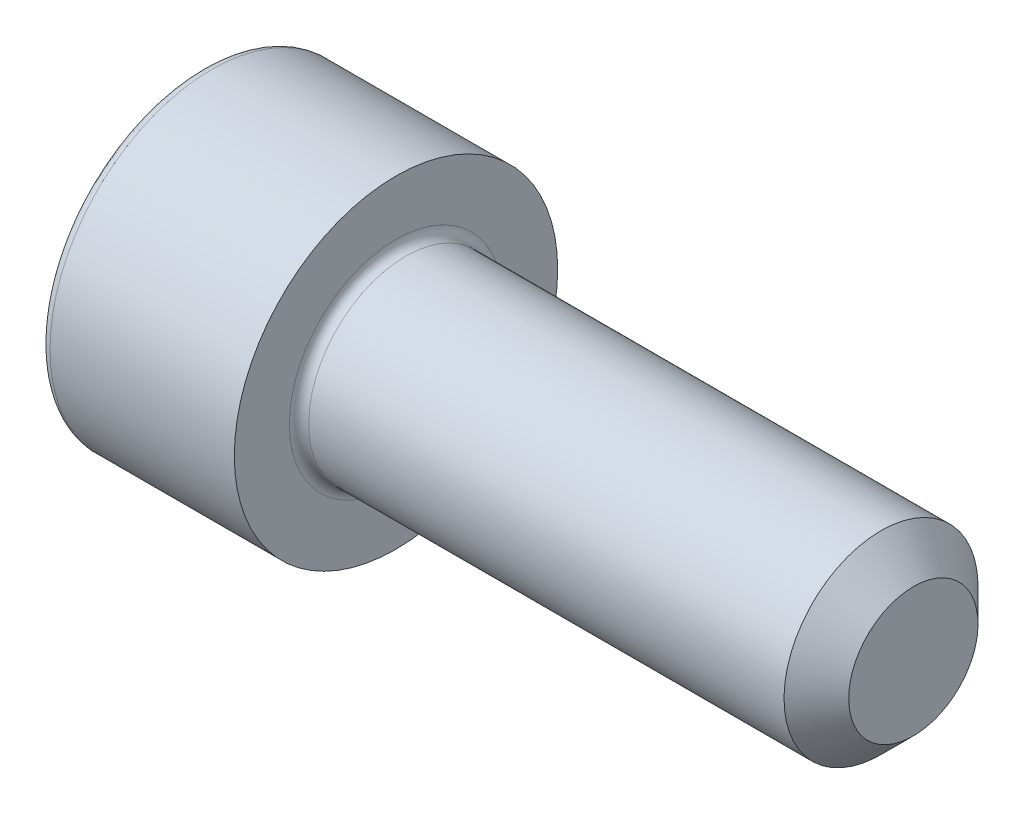
SolidWorks part; units mm, degrees
ref_plane "Спереди" through (0, 0, 0) normal (0, 0, 1) x (1, 0, 0)
ref_plane "Сверху" through (0, 0, 0) normal (0, 1, 0) x (1, 0, 0)
ref_plane "Справа" through (0, 0, 0) normal (1, 0, 0) x (0, 0, -1)
sketch "Эскиз1" plane through (0, 0, 0) normal (0, 0, 1) x (1, 0, 0)
  line L0 (0, 0) -> (0, 5)
  line L1 (0, 5) -> (6, 5)
  line L2 (6, 5) -> (6, 3)
  line L3 (6, 3) -> (22, 3)
  line L4 (22, 3) -> (22, 0)
  line L5 (22, 0) -> (0, 0) construction
  line L6 (0, 0) -> (22, 0)
  dimension "D1" = 10
  dimension "D2" = 6
  dimension "D3" = 6
  dimension "D4" = 16
revolve "Повернуть1" add sketch "Эскиз1" angle 360 about L5
cosmetic thread "Условное изображение резьбы1" parameters "D2"=4.891
sketch "Эскиз2" plane through (0, 0, 0) normal (-1, 0, 0) x (0, 0, 1)
  line L1 (-1.4434, 2.5) -> (-2.8868, 0)
  line L2 (-2.8868, 0) -> (-1.4434, -2.5)
  line L3 (-1.4434, -2.5) -> (1.4434, -2.5)
  line L4 (1.4434, -2.5) -> (2.8868, 0)
  line L5 (2.8868, 0) -> (1.4434, 2.5)
  line L6 (1.4434, 2.5) -> (-1.4434, 2.5)
  circle A0 centre (0, 0) radius 2.5 construction
  dimension "D1" = 5
extrude "Вырез-Вытянуть1" cut sketch "Эскиз2" against normal blind 2.5
fillet "Скругление1" radius 0.3 2 edges at (0, 5, 0) (6, 3, 0)
chamfer "Фаска1" distance 1 angle 45 1 edges at (22, 3, 0)
